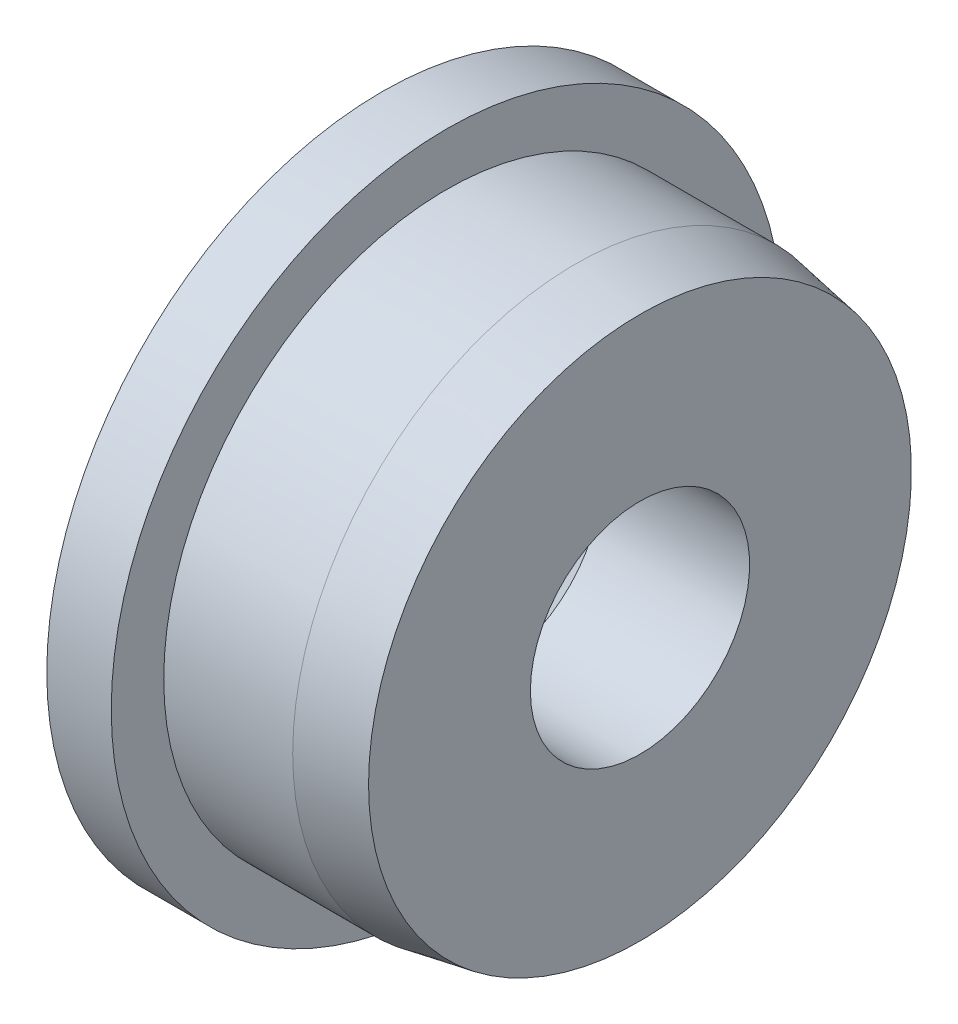
SolidWorks part; units mm, degrees
material "NITRONIC 60"
ref_plane "Front Plane" through (0, 0, 0) normal (0, 0, 1) x (1, 0, 0)
ref_plane "Top Plane" through (0, 0, 0) normal (0, 1, 0) x (1, 0, 0)
ref_plane "Right Plane" through (0, 0, 0) normal (1, 0, 0) x (0, 0, -1)
sketch "Sketch1" plane through (0, 0, 0) normal (0, 0, 1) x (1, 0, 0)
  line L0 (0, 0) -> (3.81, 0) construction
  line L1 (3.81, 2.159) -> (0.889, 2.159)
  line L2 (0.889, 2.159) -> (-1.27, 4.318)
  line L3 (-1.27, 4.318) -> (-1.27, 6.604)
  line L4 (-1.27, 6.604) -> (0, 6.604)
  line L5 (0, 6.604) -> (0, 5.5702)
  line L6 (0, 5.5702) -> (2.54, 5.5702)
  line L7 (3.81, 5.3463) -> (3.81, 2.159)
  line L8 (0.889, -2.159) -> (-1.27, -4.318) construction
  line L9 (-1.3574, 3.9688) -> (-13.5824, 3.9687) construction
  line L10 (-1.3574, -3.9688) -> (-13.5824, -3.9687) construction
  line L11 (-3.0586, 0) -> (-1.3574, 3.9688) construction
  line L12 (-3.0586, 0) -> (-0.0053, 3.0533) construction
  line L13 (2.54, 5.5702) -> (3.81, 5.3463)
  arc A0 (-1.3574, 3.9688) -> (-1.3574, -3.9688) centre (-3.0586, 0) cw construction
  dimension "D7" = 4.318
  dimension "D1" = 90
  dimension "D2" = 1.27
  dimension "D3" = 11.1404
  dimension "D4" = 4.318
  dimension "D5" = 8.636
  dimension "D6" = 7.9375
  dimension "D8" = 21.797
  dimension "D9" = 3.81
  dimension "D10" = 13.208
  dimension "D11" = 10
  dimension "D12" = 2.54
  dimension "D13" = 10.6926
revolve "Revolve1" add sketch "Sketch1" angle 360 about L0
